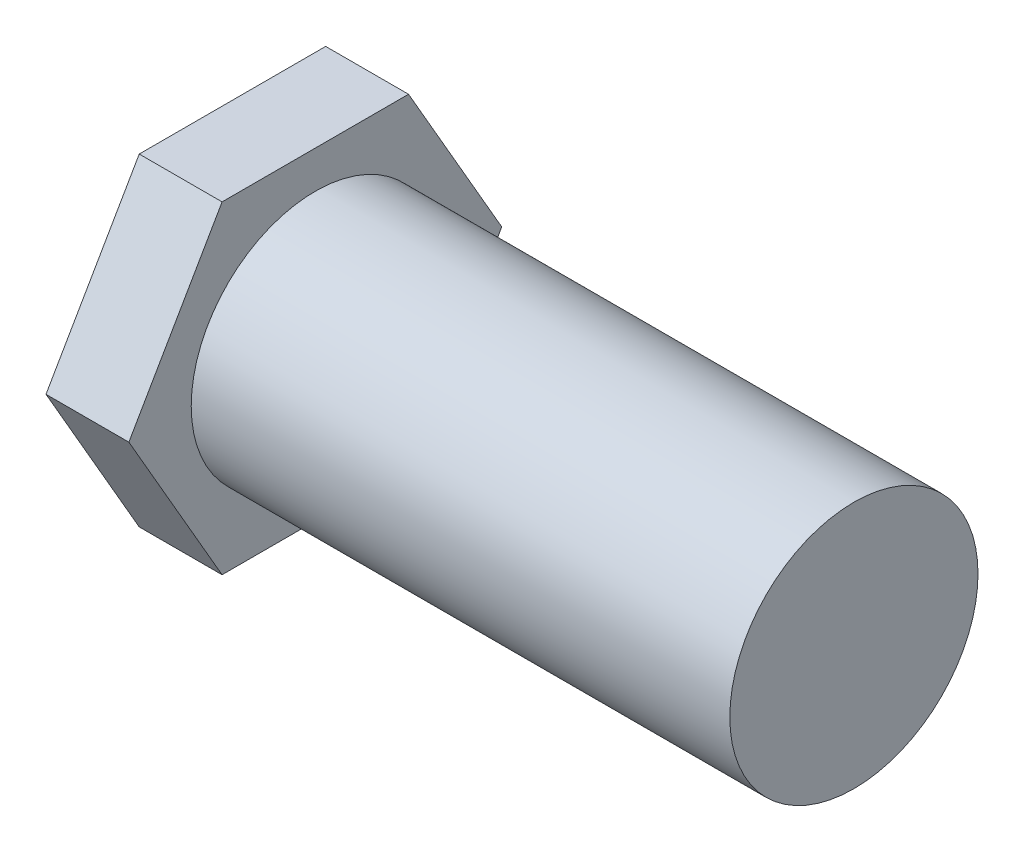
SolidWorks part; units mm, degrees
ref_plane "Front Plane" through (0, 0, 0) normal (0, 0, 1) x (1, 0, 0)
ref_plane "Top Plane" through (0, 0, 0) normal (0, 1, 0) x (1, 0, 0)
ref_plane "Right Plane" through (0, 0, 0) normal (1, 0, 0) x (0, 0, -1)
sketch "Sketch1" plane through (0, 0, 0) normal (1, 0, 0) x (0, 0, -1)
  circle A0 centre (0, 0) radius 29.95
  dimension "D1" = 59.9
extrude "Boss-Extrude1" add sketch "Sketch1" along normal blind 130
sketch "Sketch2" plane through (0, 0, 0) normal (-1, 0, 0) x (0, 0, 1)
  line L1 (45, 0) -> (22.5, 38.9711)
  line L2 (22.5, 38.9711) -> (-22.5, 38.9711)
  line L3 (-22.5, 38.9711) -> (-45, 0)
  line L4 (-45, 0) -> (-22.5, -38.9711)
  line L5 (-22.5, -38.9711) -> (22.5, -38.9711)
  line L6 (22.5, -38.9711) -> (45, 0)
  circle A0 centre (0, 0) radius 38.9711 construction
  dimension "D1" = 90
extrude "Boss-Extrude2" add sketch "Sketch2" along normal blind 20
